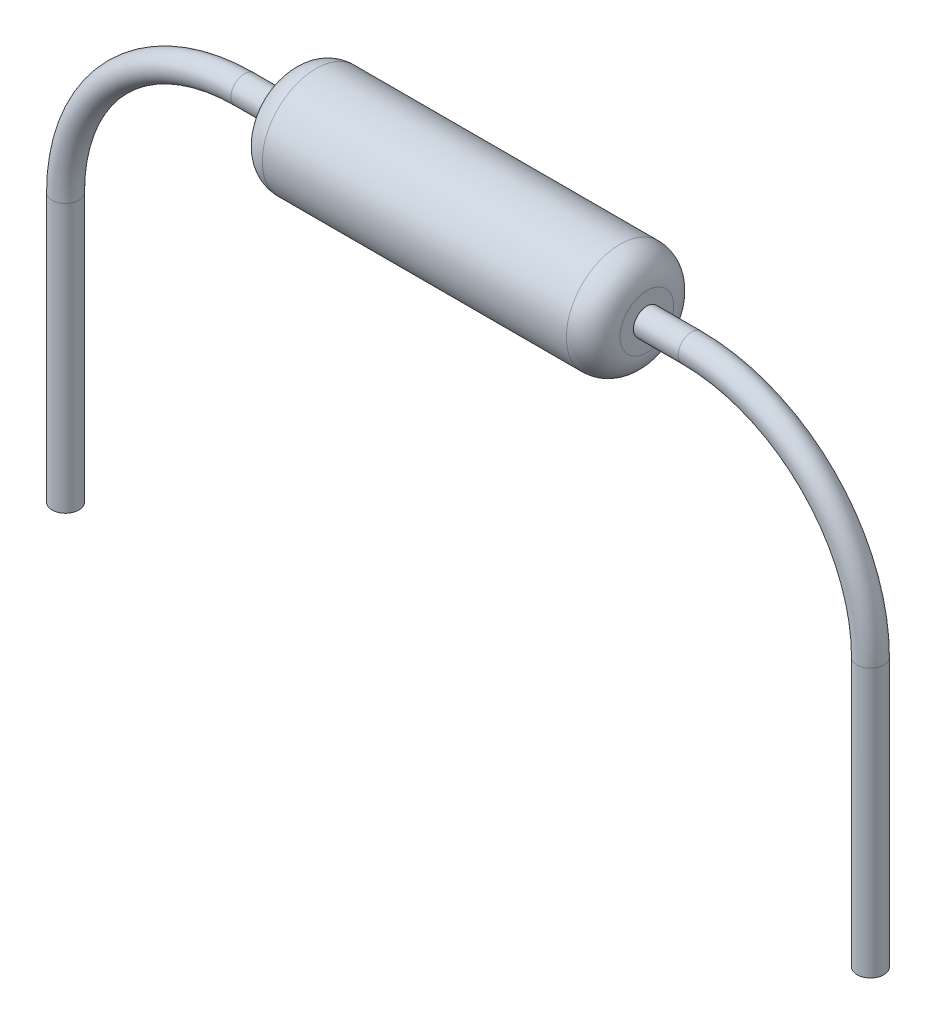
SolidWorks part; units mm, degrees
ref_plane "Front" through (0, 0, 0) normal (0, 0, 1) x (1, 0, 0)
ref_plane "Top" through (0, 0, 0) normal (0, 1, 0) x (1, 0, 0)
ref_plane "Right" through (0, 0, 0) normal (1, 0, 0) x (0, 0, -1)
sketch "Sketch1" plane through (0, 0, 0) normal (0, 0, 1) x (1, 0, 0)
  line L0 (-19.9518, 0) -> (19.9518, 0) construction
  line L1 (1.75, 0) -> (-1.75, 0)
  line L2 (-1.75, 0.35) -> (1.75, 0.35)
  line L3 (-1.75, 0.35) -> (-1.75, 0)
  line L5 (1.75, 0.35) -> (1.75, 0)
  dimension "D1" = 1.75
  dimension "D2" = 0.35
  dimension "D3" = 3.5
revolve "Base-Revolve" add sketch "Sketch1" angle 360 about L0
fillet "Fillet1" radius 0.1 2 edges at (1.75, 0, 0.35) (-1.75, 0, 0.35)
sketch "Sketch2" plane through (0, 0, 0) normal (0, 0, 1) x (1, 0, 0)
  line L0 (0.15, 0) -> (0.15, 0.55)
  line L1 (-19.9518, 0) -> (19.9518, 0) construction
  line L2 (0.15, 0.55) -> (1.25, 0.55)
  line L3 (1.25, 0.55) -> (1.25, 0)
  line L4 (1.25, 0) -> (0.15, 0)
  line L5 (0, 0) -> (1.5054, 0) construction
  line L6 (1.75, -0.25) -> (1.75, 0.25) construction
  dimension "D1" = 1.1
  dimension "D2" = 0.55
  dimension "D3" = 0.5
revolve "Boss-Revolve1" add sketch "Sketch2" angle 360 about L5
sketch "Sketch3" plane through (0, 0, 0) normal (1, 0, 0) x (0, 0, -1)
  circle A0 centre (0, -7) radius 0.15
  dimension "D1" = 0.3
  dimension "D2" = 7
sketch "Sketch4" plane through (0, 0, 0) normal (0, 0, 1) x (1, 0, 0)
  line L0 (0.174, -7) -> (-2.5, -7)
  line L1 (-4.5, -5) -> (-4.5, -2)
  line L2 (-2.5, 0) -> (2.5, 0)
  line L3 (-19.9518, 0) -> (19.9518, 0) construction
  line L4 (4.5, -2) -> (4.5, -5)
  line L5 (2.5, -7) -> (0.174, -7)
  arc A0 (-4.5, -2) -> (-2.5, 0) centre (-2.5, -2) cw
  arc A1 (4.5, -2) -> (2.5, 0) centre (2.5, -2) ccw
  arc A2 (2.5, -7) -> (4.5, -5) centre (2.5, -5) ccw
  arc A3 (-4.5, -5) -> (-2.5, -7) centre (-2.5, -5) ccw
  point P12 (4.5, 0)
  dimension "D4" = 2
  dimension "D1" = 4.5
  dimension "D2" = 9
  dimension "D3" = 7
sweep "Boss-Sweep1" add profiles "Sketch3" path "Sketch4"
sketch "Sketch5" plane through (0, 0, 0) normal (0, 0, 1) x (1, 0, 0)
  line L0 (2, 0) -> (-2.5573, 0) construction
  line L1 (-1.7, 0.6) -> (1.7, 0.6)
  line L2 (-2, 0.3) -> (-2, 0)
  line L3 (-2, 0) -> (-1.955, 0)
  line L4 (2, 0.3) -> (2, 0)
  line L5 (1.75, 0) -> (2.5, 0) construction
  line L6 (-1.955, 0.3) -> (-1.955, 0)
  line L7 (1.955, 0) -> (2, 0)
  line L8 (1.955, 0.3) -> (1.955, 0)
  line L9 (-1.7, 0.555) -> (1.7, 0.555)
  arc A0 (-2, 0.3) -> (-1.7, 0.6) centre (-1.7, 0.3) cw
  arc A1 (2, 0.3) -> (1.7, 0.6) centre (1.7, 0.3) ccw
  arc A2 (1.955, 0.3) -> (1.7, 0.555) centre (1.7, 0.3) ccw
  arc A3 (-1.955, 0.3) -> (-1.7, 0.555) centre (-1.7, 0.3) cw
  dimension "D4" = 0.3
  dimension "D5" = 0.3
  dimension "D1" = 2
  dimension "D2" = 2
  dimension "D3" = 0.6
  dimension "D6" = 0.045
revolve "Boss-Revolve2" add sketch "Sketch5" angle 360 about L0
sketch "Sketch6" plane through (0, 0, 0) normal (0, 0, 1) x (1, 0, 0)
  line L1 (-5, -5) -> (5, -5)
  line L2 (-5, -5) -> (-5, -7.5)
  line L3 (-5, -7.5) -> (5, -7.5)
  line L4 (5, -5) -> (5, -7.5)
  dimension "D1" = 5
  dimension "D2" = 2.5
  dimension "D3" = 10
  dimension "D4" = 5
extrude "Cut-Extrude1" cut sketch "Sketch6" against normal through all and the other way through all
